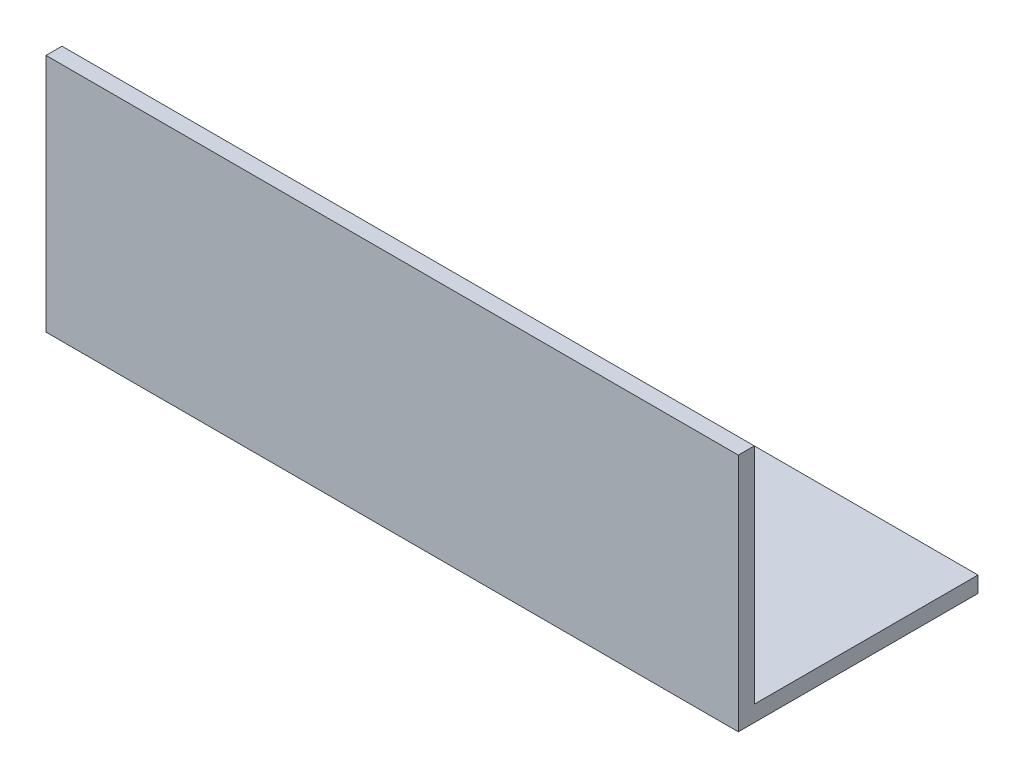
SolidWorks part; units mm, degrees
ref_plane "Спереди" through (0, 0, 0) normal (0, 0, 1) x (1, 0, 0)
ref_plane "Сверху" through (0, 0, 0) normal (0, 1, 0) x (1, 0, 0)
ref_plane "Справа" through (0, 0, 0) normal (1, 0, 0) x (0, 0, -1)
sketch "Эскиз1" plane through (0, 0, 0) normal (1, 0, 0) x (0, 0, -1)
  line L0 (0, 0) -> (0, 45)
  line L1 (0, 0) -> (45, 0)
  dimension "D1" = 45
extrude "Вытянуть-Тонкостенный1" add sketch "Эскиз1" along normal blind 130 thin
